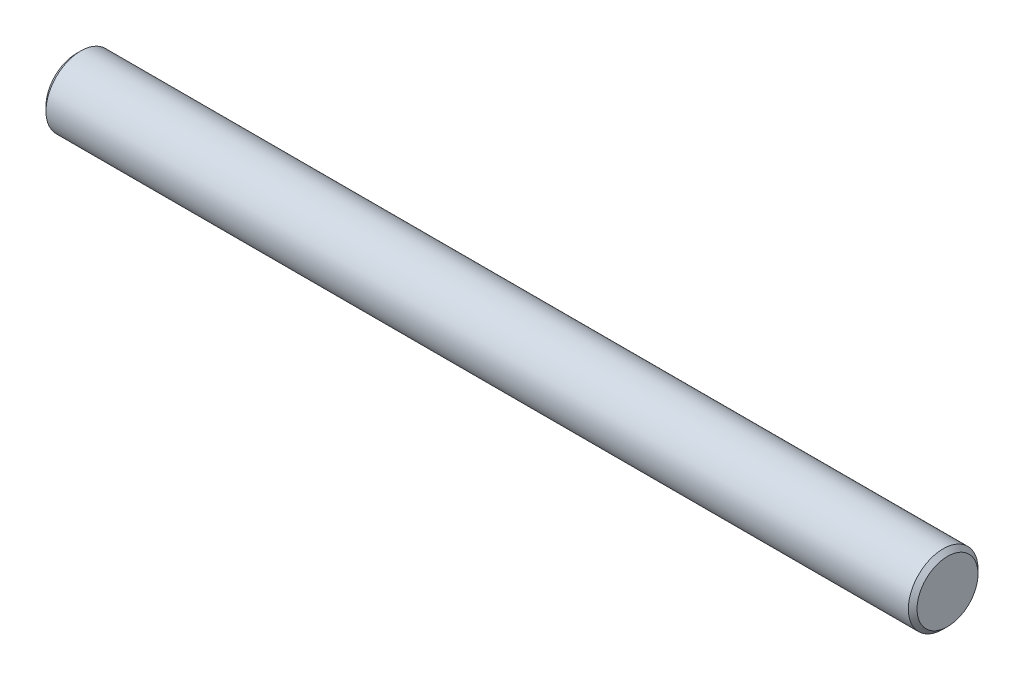
SolidWorks part; units mm, degrees
material "Stainless Steel (ferritic)"
ref_plane "Front Plane" through (0, 0, 0) normal (0, 0, 1) x (1, 0, 0)
ref_plane "Top Plane" through (0, 0, 0) normal (0, 1, 0) x (1, 0, 0)
ref_plane "Right Plane" through (0, 0, 0) normal (1, 0, 0) x (0, 0, -1)
sketch "Sketch1" plane through (0, 0, 0) normal (1, 0, 0) x (0, -1, 0)
  circle A0 centre (0, 0) radius 4
  dimension "D1" = 8
extrude "Boss-Extrude1" add sketch "Sketch1" along normal mid plane 100
chamfer "Chamfer1" distance 0.5 angle 45 2 edges at (-50, 0, -4) (50, 0, -4)
